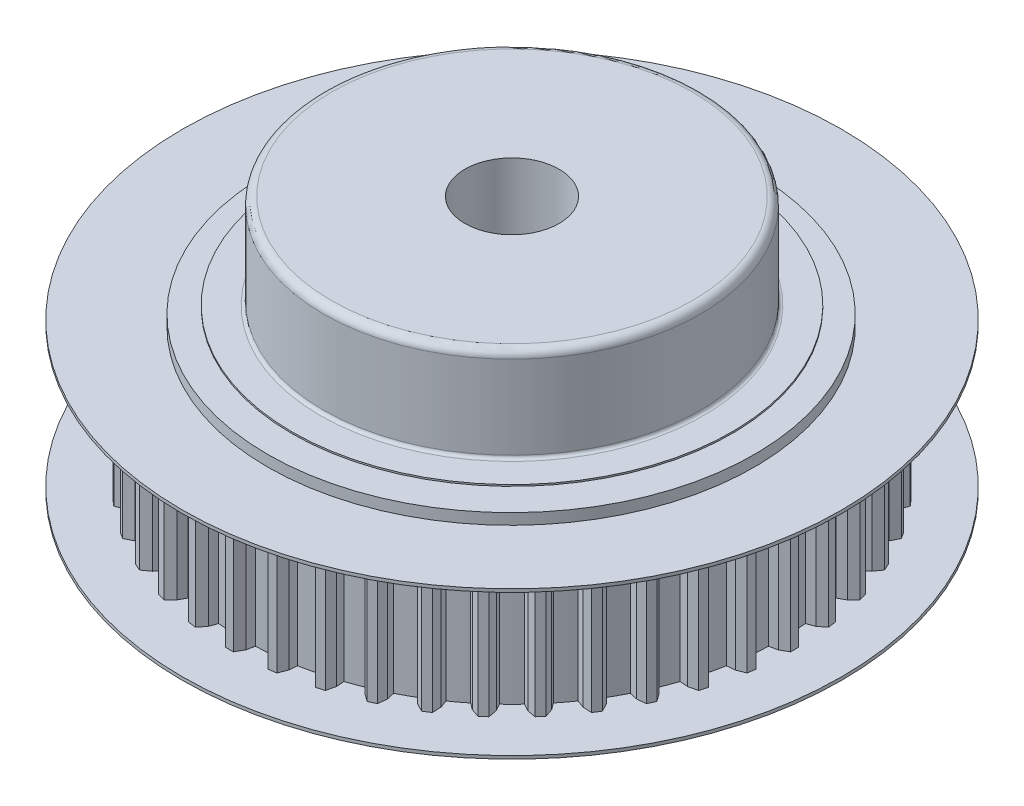
SolidWorks part; units mm, degrees
material "Alliage 1060"
ref_plane "Plan de face" through (0, 0, 0) normal (0, 0, 1) x (1, 0, 0)
ref_plane "Plan de dessus" through (0, 0, 0) normal (0, 1, 0) x (1, 0, 0)
ref_plane "Plan de droite" through (0, 0, 0) normal (1, 0, 0) x (0, 0, -1)
sketch "Esquisse1" plane through (0, 0, 0) normal (0, 1, 0) x (1, 0, 0)
  circle A0 centre (0, 0) radius 17
  dimension "D1" = 34
extrude "Boss.-Extru.1" add sketch "Esquisse1" along normal blind 9
sketch "Esquisse2" plane through (0, 9, 0) normal (0, 1, 0) x (1, 0, 0)
  line L0 (-0.25, 18) -> (0.25, 18)
  line L1 (0.25, 18) -> (0.5387, 17.5)
  line L2 (0.5387, 17.5) -> (0.65, 16.9876)
  line L3 (-0.25, 18) -> (-0.5435, 17.4916)
  line L4 (-0.5435, 17.4916) -> (-0.65, 16.9876)
  line L5 (-0.65, 16.9876) -> (0.65, 16.9876)
  line L6 (2.3142, 17.8524) -> (2.8091, 17.7812)
  line L7 (2.8091, 17.7812) -> (3.0237, 17.2452)
  line L8 (3.0237, 17.2452) -> (3.061, 16.7222)
  line L9 (2.3142, 17.8524) -> (1.9513, 17.3909)
  line L10 (1.9513, 17.3909) -> (1.7742, 16.9072)
  line L11 (1.7742, 16.9072) -> (3.061, 16.7222)
  line L12 (4.8313, 17.3413) -> (5.3111, 17.2004)
  line L13 (5.3111, 17.2004) -> (5.4472, 16.6394)
  line L14 (5.4472, 16.6394) -> (5.4096, 16.1163)
  line L15 (4.8313, 17.3413) -> (4.4064, 16.9362)
  line L16 (4.4064, 16.9362) -> (4.1623, 16.4826)
  line L17 (4.1623, 16.4826) -> (5.4096, 16.1163)
  line L18 (7.2501, 16.4772) -> (7.7049, 16.2695)
  line L19 (7.7049, 16.2695) -> (7.7598, 15.6948)
  line L20 (7.7598, 15.6948) -> (7.6482, 15.1824)
  line L21 (7.2501, 16.4772) -> (6.7718, 16.1367)
  line L22 (6.7718, 16.1367) -> (6.4656, 15.7225)
  line L23 (6.4656, 15.7225) -> (7.6482, 15.1824)
  line L24 (9.5212, 15.2777) -> (9.9418, 15.0074)
  line L25 (9.9418, 15.0074) -> (9.9144, 14.4307)
  line L26 (9.9144, 14.4307) -> (9.731, 13.9394)
  line L27 (9.5212, 15.2777) -> (8.9994, 15.0087)
  line L28 (8.9994, 15.0087) -> (8.6374, 14.6423)
  line L29 (8.6374, 14.6423) -> (9.731, 13.9394)
  line L30 (11.5986, 13.7672) -> (11.9764, 13.4398)
  line L31 (11.9764, 13.4398) -> (11.8672, 12.8729)
  line L32 (11.8672, 12.8729) -> (11.6157, 12.4127)
  line L33 (11.5986, 13.7672) -> (11.0437, 13.5752)
  line L34 (11.0437, 13.5752) -> (10.6333, 13.264)
  line L35 (10.6333, 13.264) -> (11.6157, 12.4127)
  line L36 (13.4398, 11.9764) -> (13.7672, 11.5986)
  line L37 (13.7672, 11.5986) -> (13.5784, 11.053)
  line L38 (13.5784, 11.053) -> (13.264, 10.6333)
  line L39 (13.4398, 11.9764) -> (12.8633, 11.8653)
  line L40 (12.8633, 11.8653) -> (12.4127, 11.6157)
  line L41 (12.4127, 11.6157) -> (13.264, 10.6333)
  line L42 (15.0074, 9.9418) -> (15.2777, 9.5212)
  line L43 (15.2777, 9.5212) -> (15.0132, 9.0081)
  line L44 (15.0132, 9.0081) -> (14.6423, 8.6374)
  line L45 (15.0074, 9.9418) -> (14.421, 9.9139)
  line L46 (14.421, 9.9139) -> (13.9394, 9.731)
  line L47 (13.9394, 9.731) -> (14.6423, 8.6374)
  line L48 (16.2695, 7.7049) -> (16.4772, 7.2501)
  line L49 (16.4772, 7.2501) -> (16.1423, 6.7798)
  line L50 (16.1423, 6.7798) -> (15.7225, 6.4656)
  line L51 (16.2695, 7.7049) -> (15.6851, 7.7607)
  line L52 (15.6851, 7.7607) -> (15.1824, 7.6482)
  line L53 (15.1824, 7.6482) -> (15.7225, 6.4656)
  line L54 (17.2004, 5.3111) -> (17.3413, 4.8313)
  line L55 (17.3413, 4.8313) -> (16.9429, 4.4135)
  line L56 (16.9429, 4.4135) -> (16.4826, 4.1623)
  line L57 (17.2004, 5.3111) -> (16.6299, 5.4495)
  line L58 (16.6299, 5.4495) -> (16.1163, 5.4096)
  line L59 (16.1163, 5.4096) -> (16.4826, 4.1623)
  line L60 (17.7812, 2.8091) -> (17.8524, 2.3142)
  line L61 (17.8524, 2.3142) -> (17.3985, 1.9573)
  line L62 (17.3985, 1.9573) -> (16.9072, 1.7742)
  line L63 (17.7812, 2.8091) -> (17.2362, 3.0273)
  line L64 (17.2362, 3.0273) -> (16.7222, 3.061)
  line L65 (16.7222, 3.061) -> (16.9072, 1.7742)
  line L66 (18, 0.25) -> (18, -0.25)
  line L67 (18, -0.25) -> (17.5, -0.5387)
  line L68 (17.5, -0.5387) -> (16.9876, -0.65)
  line L69 (18, 0.25) -> (17.4916, 0.5435)
  line L70 (17.4916, 0.5435) -> (16.9876, 0.65)
  line L71 (16.9876, 0.65) -> (16.9876, -0.65)
  line L72 (17.8524, -2.3142) -> (17.7812, -2.8091)
  line L73 (17.7812, -2.8091) -> (17.2452, -3.0237)
  line L74 (17.2452, -3.0237) -> (16.7222, -3.061)
  line L75 (17.8524, -2.3142) -> (17.3909, -1.9513)
  line L76 (17.3909, -1.9513) -> (16.9072, -1.7742)
  line L77 (16.9072, -1.7742) -> (16.7222, -3.061)
  line L78 (17.3413, -4.8313) -> (17.2004, -5.3111)
  line L79 (17.2004, -5.3111) -> (16.6394, -5.4472)
  line L80 (16.6394, -5.4472) -> (16.1163, -5.4096)
  line L81 (17.3413, -4.8313) -> (16.9362, -4.4064)
  line L82 (16.9362, -4.4064) -> (16.4826, -4.1623)
  line L83 (16.4826, -4.1623) -> (16.1163, -5.4096)
  line L84 (16.4772, -7.2501) -> (16.2695, -7.7049)
  line L85 (16.2695, -7.7049) -> (15.6948, -7.7598)
  line L86 (15.6948, -7.7598) -> (15.1824, -7.6482)
  line L87 (16.4772, -7.2501) -> (16.1367, -6.7718)
  line L88 (16.1367, -6.7718) -> (15.7225, -6.4656)
  line L89 (15.7225, -6.4656) -> (15.1824, -7.6482)
  line L90 (15.2777, -9.5212) -> (15.0074, -9.9418)
  line L91 (15.0074, -9.9418) -> (14.4307, -9.9144)
  line L92 (14.4307, -9.9144) -> (13.9394, -9.731)
  line L93 (15.2777, -9.5212) -> (15.0087, -8.9994)
  line L94 (15.0087, -8.9994) -> (14.6423, -8.6374)
  line L95 (14.6423, -8.6374) -> (13.9394, -9.731)
  line L96 (13.7672, -11.5986) -> (13.4398, -11.9764)
  line L97 (13.4398, -11.9764) -> (12.8729, -11.8672)
  line L98 (12.8729, -11.8672) -> (12.4127, -11.6157)
  line L99 (13.7672, -11.5986) -> (13.5752, -11.0437)
  line L100 (13.5752, -11.0437) -> (13.264, -10.6333)
  line L101 (13.264, -10.6333) -> (12.4127, -11.6157)
  line L102 (11.9764, -13.4398) -> (11.5986, -13.7672)
  line L103 (11.5986, -13.7672) -> (11.053, -13.5784)
  line L104 (11.053, -13.5784) -> (10.6333, -13.264)
  line L105 (11.9764, -13.4398) -> (11.8653, -12.8633)
  line L106 (11.8653, -12.8633) -> (11.6157, -12.4127)
  line L107 (11.6157, -12.4127) -> (10.6333, -13.264)
  line L108 (9.9418, -15.0074) -> (9.5212, -15.2777)
  line L109 (9.5212, -15.2777) -> (9.0081, -15.0132)
  line L110 (9.0081, -15.0132) -> (8.6374, -14.6423)
  line L111 (9.9418, -15.0074) -> (9.9139, -14.421)
  line L112 (9.9139, -14.421) -> (9.731, -13.9394)
  line L113 (9.731, -13.9394) -> (8.6374, -14.6423)
  line L114 (7.7049, -16.2695) -> (7.2501, -16.4772)
  line L115 (7.2501, -16.4772) -> (6.7798, -16.1423)
  line L116 (6.7798, -16.1423) -> (6.4656, -15.7225)
  line L117 (7.7049, -16.2695) -> (7.7607, -15.6851)
  line L118 (7.7607, -15.6851) -> (7.6482, -15.1824)
  line L119 (7.6482, -15.1824) -> (6.4656, -15.7225)
  line L120 (5.3111, -17.2004) -> (4.8313, -17.3413)
  line L121 (4.8313, -17.3413) -> (4.4135, -16.9429)
  line L122 (4.4135, -16.9429) -> (4.1623, -16.4826)
  line L123 (5.3111, -17.2004) -> (5.4495, -16.6299)
  line L124 (5.4495, -16.6299) -> (5.4096, -16.1163)
  line L125 (5.4096, -16.1163) -> (4.1623, -16.4826)
  line L126 (2.8091, -17.7812) -> (2.3142, -17.8524)
  line L127 (2.3142, -17.8524) -> (1.9573, -17.3985)
  line L128 (1.9573, -17.3985) -> (1.7742, -16.9072)
  line L129 (2.8091, -17.7812) -> (3.0273, -17.2362)
  line L130 (3.0273, -17.2362) -> (3.061, -16.7222)
  line L131 (3.061, -16.7222) -> (1.7742, -16.9072)
  line L132 (0.25, -18) -> (-0.25, -18)
  line L133 (-0.25, -18) -> (-0.5387, -17.5)
  line L134 (-0.5387, -17.5) -> (-0.65, -16.9876)
  line L135 (0.25, -18) -> (0.5435, -17.4916)
  line L136 (0.5435, -17.4916) -> (0.65, -16.9876)
  line L137 (0.65, -16.9876) -> (-0.65, -16.9876)
  line L138 (-2.3142, -17.8524) -> (-2.8091, -17.7812)
  line L139 (-2.8091, -17.7812) -> (-3.0237, -17.2452)
  line L140 (-3.0237, -17.2452) -> (-3.061, -16.7222)
  line L141 (-2.3142, -17.8524) -> (-1.9513, -17.3909)
  line L142 (-1.9513, -17.3909) -> (-1.7742, -16.9072)
  line L143 (-1.7742, -16.9072) -> (-3.061, -16.7222)
  line L144 (-4.8313, -17.3413) -> (-5.3111, -17.2004)
  line L145 (-5.3111, -17.2004) -> (-5.4472, -16.6394)
  line L146 (-5.4472, -16.6394) -> (-5.4096, -16.1163)
  line L147 (-4.8313, -17.3413) -> (-4.4064, -16.9362)
  line L148 (-4.4064, -16.9362) -> (-4.1623, -16.4826)
  line L149 (-4.1623, -16.4826) -> (-5.4096, -16.1163)
  line L150 (-7.2501, -16.4772) -> (-7.7049, -16.2695)
  line L151 (-7.7049, -16.2695) -> (-7.7598, -15.6948)
  line L152 (-7.7598, -15.6948) -> (-7.6482, -15.1824)
  line L153 (-7.2501, -16.4772) -> (-6.7718, -16.1367)
  line L154 (-6.7718, -16.1367) -> (-6.4656, -15.7225)
  line L155 (-6.4656, -15.7225) -> (-7.6482, -15.1824)
  line L156 (-9.5212, -15.2777) -> (-9.9418, -15.0074)
  line L157 (-9.9418, -15.0074) -> (-9.9144, -14.4307)
  line L158 (-9.9144, -14.4307) -> (-9.731, -13.9394)
  line L159 (-9.5212, -15.2777) -> (-8.9994, -15.0087)
  line L160 (-8.9994, -15.0087) -> (-8.6374, -14.6423)
  line L161 (-8.6374, -14.6423) -> (-9.731, -13.9394)
  line L162 (-11.5986, -13.7672) -> (-11.9764, -13.4398)
  line L163 (-11.9764, -13.4398) -> (-11.8672, -12.8729)
  line L164 (-11.8672, -12.8729) -> (-11.6157, -12.4127)
  line L165 (-11.5986, -13.7672) -> (-11.0437, -13.5752)
  line L166 (-11.0437, -13.5752) -> (-10.6333, -13.264)
  line L167 (-10.6333, -13.264) -> (-11.6157, -12.4127)
  line L168 (-13.4398, -11.9764) -> (-13.7672, -11.5986)
  line L169 (-13.7672, -11.5986) -> (-13.5784, -11.053)
  line L170 (-13.5784, -11.053) -> (-13.264, -10.6333)
  line L171 (-13.4398, -11.9764) -> (-12.8633, -11.8653)
  line L172 (-12.8633, -11.8653) -> (-12.4127, -11.6157)
  line L173 (-12.4127, -11.6157) -> (-13.264, -10.6333)
  line L174 (-15.0074, -9.9418) -> (-15.2777, -9.5212)
  line L175 (-15.2777, -9.5212) -> (-15.0132, -9.0081)
  line L176 (-15.0132, -9.0081) -> (-14.6423, -8.6374)
  line L177 (-15.0074, -9.9418) -> (-14.421, -9.9139)
  line L178 (-14.421, -9.9139) -> (-13.9394, -9.731)
  line L179 (-13.9394, -9.731) -> (-14.6423, -8.6374)
  line L180 (-16.2695, -7.7049) -> (-16.4772, -7.2501)
  line L181 (-16.4772, -7.2501) -> (-16.1423, -6.7798)
  line L182 (-16.1423, -6.7798) -> (-15.7225, -6.4656)
  line L183 (-16.2695, -7.7049) -> (-15.6851, -7.7607)
  line L184 (-15.6851, -7.7607) -> (-15.1824, -7.6482)
  line L185 (-15.1824, -7.6482) -> (-15.7225, -6.4656)
  line L186 (-17.2004, -5.3111) -> (-17.3413, -4.8313)
  line L187 (-17.3413, -4.8313) -> (-16.9429, -4.4135)
  line L188 (-16.9429, -4.4135) -> (-16.4826, -4.1623)
  line L189 (-17.2004, -5.3111) -> (-16.6299, -5.4495)
  line L190 (-16.6299, -5.4495) -> (-16.1163, -5.4096)
  line L191 (-16.1163, -5.4096) -> (-16.4826, -4.1623)
  line L192 (-17.7812, -2.8091) -> (-17.8524, -2.3142)
  line L193 (-17.8524, -2.3142) -> (-17.3985, -1.9573)
  line L194 (-17.3985, -1.9573) -> (-16.9072, -1.7742)
  line L195 (-17.7812, -2.8091) -> (-17.2362, -3.0273)
  line L196 (-17.2362, -3.0273) -> (-16.7222, -3.061)
  line L197 (-16.7222, -3.061) -> (-16.9072, -1.7742)
  line L198 (-18, -0.25) -> (-18, 0.25)
  line L199 (-18, 0.25) -> (-17.5, 0.5387)
  line L200 (-17.5, 0.5387) -> (-16.9876, 0.65)
  line L201 (-18, -0.25) -> (-17.4916, -0.5435)
  line L202 (-17.4916, -0.5435) -> (-16.9876, -0.65)
  line L203 (-16.9876, -0.65) -> (-16.9876, 0.65)
  line L204 (-17.8524, 2.3142) -> (-17.7812, 2.8091)
  line L205 (-17.7812, 2.8091) -> (-17.2452, 3.0237)
  line L206 (-17.2452, 3.0237) -> (-16.7222, 3.061)
  line L207 (-17.8524, 2.3142) -> (-17.3909, 1.9513)
  line L208 (-17.3909, 1.9513) -> (-16.9072, 1.7742)
  line L209 (-16.9072, 1.7742) -> (-16.7222, 3.061)
  line L210 (-17.3413, 4.8313) -> (-17.2004, 5.3111)
  line L211 (-17.2004, 5.3111) -> (-16.6394, 5.4472)
  line L212 (-16.6394, 5.4472) -> (-16.1163, 5.4096)
  line L213 (-17.3413, 4.8313) -> (-16.9362, 4.4064)
  line L214 (-16.9362, 4.4064) -> (-16.4826, 4.1623)
  line L215 (-16.4826, 4.1623) -> (-16.1163, 5.4096)
  line L216 (-16.4772, 7.2501) -> (-16.2695, 7.7049)
  line L217 (-16.2695, 7.7049) -> (-15.6948, 7.7598)
  line L218 (-15.6948, 7.7598) -> (-15.1824, 7.6482)
  line L219 (-16.4772, 7.2501) -> (-16.1367, 6.7718)
  line L220 (-16.1367, 6.7718) -> (-15.7225, 6.4656)
  line L221 (-15.7225, 6.4656) -> (-15.1824, 7.6482)
  line L222 (-15.2777, 9.5212) -> (-15.0074, 9.9418)
  line L223 (-15.0074, 9.9418) -> (-14.4307, 9.9144)
  line L224 (-14.4307, 9.9144) -> (-13.9394, 9.731)
  line L225 (-15.2777, 9.5212) -> (-15.0087, 8.9994)
  line L226 (-15.0087, 8.9994) -> (-14.6423, 8.6374)
  line L227 (-14.6423, 8.6374) -> (-13.9394, 9.731)
  line L228 (-13.7672, 11.5986) -> (-13.4398, 11.9764)
  line L229 (-13.4398, 11.9764) -> (-12.8729, 11.8672)
  line L230 (-12.8729, 11.8672) -> (-12.4127, 11.6157)
  line L231 (-13.7672, 11.5986) -> (-13.5752, 11.0437)
  line L232 (-13.5752, 11.0437) -> (-13.264, 10.6333)
  line L233 (-13.264, 10.6333) -> (-12.4127, 11.6157)
  line L234 (-11.9764, 13.4398) -> (-11.5986, 13.7672)
  line L235 (-11.5986, 13.7672) -> (-11.053, 13.5784)
  line L236 (-11.053, 13.5784) -> (-10.6333, 13.264)
  line L237 (-11.9764, 13.4398) -> (-11.8653, 12.8633)
  line L238 (-11.8653, 12.8633) -> (-11.6157, 12.4127)
  line L239 (-11.6157, 12.4127) -> (-10.6333, 13.264)
  line L240 (-9.9418, 15.0074) -> (-9.5212, 15.2777)
  line L241 (-9.5212, 15.2777) -> (-9.0081, 15.0132)
  line L242 (-9.0081, 15.0132) -> (-8.6374, 14.6423)
  line L243 (-9.9418, 15.0074) -> (-9.9139, 14.421)
  line L244 (-9.9139, 14.421) -> (-9.731, 13.9394)
  line L245 (-9.731, 13.9394) -> (-8.6374, 14.6423)
  line L246 (-7.7049, 16.2695) -> (-7.2501, 16.4772)
  line L247 (-7.2501, 16.4772) -> (-6.7798, 16.1423)
  line L248 (-6.7798, 16.1423) -> (-6.4656, 15.7225)
  line L249 (-7.7049, 16.2695) -> (-7.7607, 15.6851)
  line L250 (-7.7607, 15.6851) -> (-7.6482, 15.1824)
  line L251 (-7.6482, 15.1824) -> (-6.4656, 15.7225)
  line L252 (-5.3111, 17.2004) -> (-4.8313, 17.3413)
  line L253 (-4.8313, 17.3413) -> (-4.4135, 16.9429)
  line L254 (-4.4135, 16.9429) -> (-4.1623, 16.4826)
  line L255 (-5.3111, 17.2004) -> (-5.4495, 16.6299)
  line L256 (-5.4495, 16.6299) -> (-5.4096, 16.1163)
  line L257 (-5.4096, 16.1163) -> (-4.1623, 16.4826)
  line L258 (-2.8091, 17.7812) -> (-2.3142, 17.8524)
  line L259 (-2.3142, 17.8524) -> (-1.9573, 17.3985)
  line L260 (-1.9573, 17.3985) -> (-1.7742, 16.9072)
  line L261 (-2.8091, 17.7812) -> (-3.0273, 17.2362)
  line L262 (-3.0273, 17.2362) -> (-3.061, 16.7222)
  line L263 (-3.061, 16.7222) -> (-1.7742, 16.9072)
  circle A0 centre (0, 0) radius 17 construction
  point P269 (0, 0)
  dimension "D1" = 0.5
  dimension "D2" = 18
  dimension "D3" = 120
  dimension "D4" = 120
  dimension "D5" = 17.5
  dimension "D6" = 17.5
  dimension "D7" = 0.4
  dimension "D8" = 0.4
  dimension "D9" = 0
  dimension "D10" = 44
extrude "Boss.-Extru.3" add sketch "Esquisse2" against normal blind 9
sketch "Esquisse3" plane through (0, 9, 0) normal (0, 1, 0) x (1, 0, 0)
  circle A0 centre (0, 0) radius 21
  dimension "D1" = 42
extrude "Boss.-Extru.4" add sketch "Esquisse3" along normal blind 0.2
sketch "Esquisse4" plane through (0, 9.2, 0) normal (0, 1, 0) x (1, 0, 0)
  circle A0 centre (0.3577, -0.4174) radius 15.5
  dimension "D1" = 31
extrude "Boss.-Extru.5" add sketch "Esquisse4" along normal blind 0.7
sketch "Esquisse5" plane through (0, 9.9, 0) normal (0, 1, 0) x (1, 0, 0)
  circle A0 centre (0, 0) radius 14
  dimension "D1" = 28
extrude "Boss.-Extru.6" add sketch "Esquisse5" along normal blind 0.1
sketch "Esquisse6" plane through (0, 0, 0) normal (0, -1, 0) x (1, 0, 0)
  circle A0 centre (0, 0) radius 21
  dimension "D1" = 42
extrude "Boss.-Extru.7" add sketch "Esquisse6" along normal blind 0.2
sketch "Esquisse7" plane through (0, -0.2, 0) normal (0, -1, 0) x (-1, 0, 0)
  circle A0 centre (0, 0) radius 15.5
  dimension "D1" = 31
extrude "Boss.-Extru.8" add sketch "Esquisse7" along normal blind 0.7
sketch "Esquisse8" plane through (0, -0.9, 0) normal (0, -1, 0) x (-1, 0, 0)
  circle A0 centre (0, 0) radius 14
  dimension "D1" = 28
extrude "Boss.-Extru.9" add sketch "Esquisse8" along normal blind 0.1
sketch "Esquisse9" plane through (0, 10, 0) normal (0, 1, 0) x (1, 0, 0)
  circle A0 centre (0, 0) radius 12
  dimension "D1" = 24
extrude "Boss.-Extru.10" add sketch "Esquisse9" along normal blind 6
fillet "Congé1" radius 0.5 1 edges at (0, 16, 12)
fillet "Congé2" radius 0.2 1 edges at (0, 10, 12)
sketch "Esquisse10" plane through (0, 16, 0) normal (0, 1, 0) x (1, 0, 0)
  circle A0 centre (0, 0) radius 3
  dimension "D1" = 6
extrude "Enlèv. mat.-Extru.1" cut sketch "Esquisse10" against normal through all
